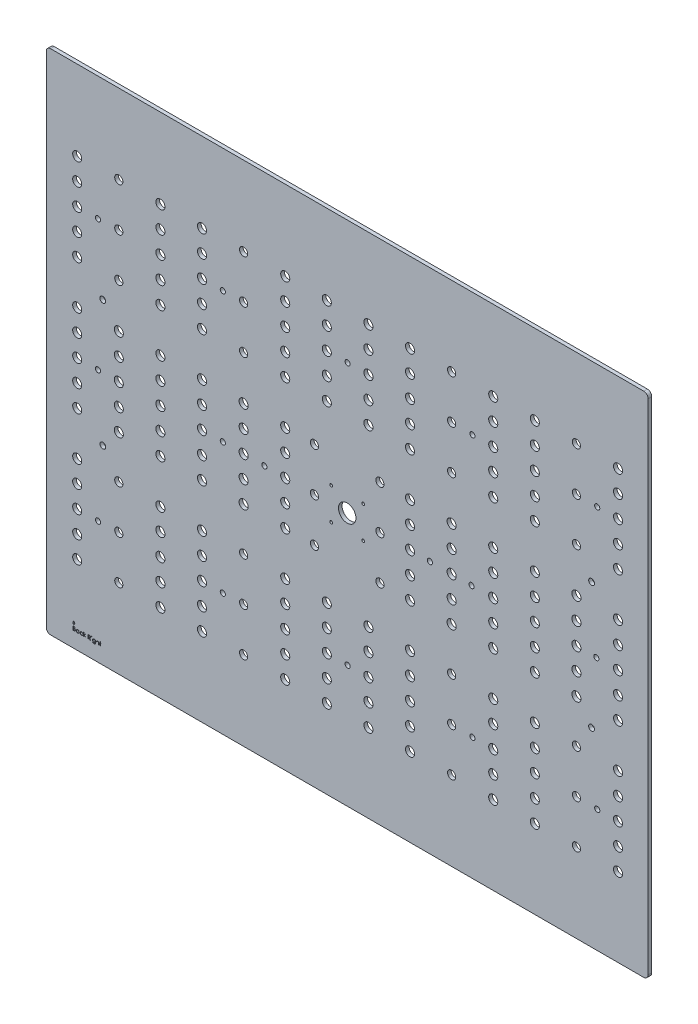
SolidWorks part; units mm, degrees
material "Acrylic (Medium-high impact)"
ref_plane "Front Plane" through (0, 0, 0) normal (0, 0, 1) x (1, 0, 0)
ref_plane "Top Plane" through (0, 0, 0) normal (0, 1, 0) x (1, 0, 0)
ref_plane "Right Plane" through (0, 0, 0) normal (1, 0, 0) x (0, 0, -1)
sketch "Sketch1" plane through (0, 0, 0) normal (0, 0, 1) x (1, 0, 0)
  line L1 (-119.7736, 224.7428) -> (458.2796, 224.7428)
  line L2 (-119.7736, 224.7428) -> (-119.7736, -271.111)
  line L3 (-119.7736, -271.111) -> (458.2796, -271.111)
  line L4 (458.2796, 224.7428) -> (458.2796, -271.111)
  dimension "D1" = 495.8537
  dimension "D2" = 578.0532
extrude "Boss-Extrude1" add sketch "Sketch1" along normal blind 3.175
sketch "Sketch8" plane through (0, 0, 3.175) normal (0, 0, 1) x (1, 0, 0)
  line L1 (-119.7736, 224.7428) -> (-100.3426, 224.7428)
  line L2 (-119.7736, 224.7428) -> (-119.7736, 205.3118)
  line L3 (-119.7736, 205.3118) -> (-100.3426, 205.3118)
  line L4 (-100.3426, 224.7428) -> (-100.3426, 205.3118)
  line L5 (458.2796, 224.7428) -> (438.8486, 224.7428)
  line L6 (458.2796, 224.7428) -> (458.2796, 205.3118)
  line L7 (458.2796, 205.3118) -> (438.8486, 205.3118)
  line L8 (438.8486, 224.7428) -> (438.8486, 205.3118)
  line L9 (458.2796, -271.111) -> (438.8486, -271.111)
  line L10 (458.2796, -271.111) -> (458.2796, -251.68)
  line L11 (458.2796, -251.68) -> (438.8486, -251.68)
  line L12 (438.8486, -271.111) -> (438.8486, -251.68)
  line L13 (-119.7736, -271.111) -> (-100.3426, -271.111)
  line L14 (-119.7736, -271.111) -> (-119.7736, -251.68)
  line L15 (-119.7736, -251.68) -> (-100.3426, -251.68)
  line L16 (-100.3426, -271.111) -> (-100.3426, -251.68)
  dimension "D1" = 19.431
extrude "Corners" cut sketch "Sketch8" against normal through all
sketch "Sketch9" plane through (0, 0, 3.175) normal (0, 0, 1) x (1, 0, 0)
  line L0 (-84.747, 138.1059) -> (423.253, 138.1059) construction
  line L1 (169.253, 224.7428) -> (169.253, -271.111) construction
  line L2 (438.8486, 224.7428) -> (-100.3426, 224.7428) construction
  line L3 (-100.3426, -271.111) -> (438.8486, -271.111) construction
  line L4 (140.678, 23.8059) -> (197.828, 23.8059) construction
  line L6 (-84.747, -213.6841) -> (423.253, -213.6841) construction
  line L7 (-84.747, -213.6841) -> (-84.747, 167.3159) construction
  line L8 (-84.747, 167.3159) -> (423.253, 167.3159) construction
  line L9 (423.253, -213.6841) -> (423.253, 167.3159) construction
  point P99 (169.253, 23.8059)
  dimension "D1" = 381
  dimension "D2" = 508
  dimension "D3" = 29.21
  dimension "D8" = 57.15
sketch "Sketch13" plane through (0, 0, 3.175) normal (0, 0, 1) x (1, 0, 0)
  line L0 (169.253, 224.7428) -> (169.253, -271.111) construction
  line L1 (438.8486, 224.7428) -> (-100.3426, 224.7428) construction
  line L2 (-100.3426, -271.111) -> (438.8486, -271.111) construction
  line L4 (155.283, -37.1541) -> (183.223, -37.1541) construction
  line L5 (155.283, -37.1541) -> (155.283, -9.2141) construction
  line L6 (155.283, -9.2141) -> (183.223, -9.2141) construction
  line L7 (183.223, -37.1541) -> (183.223, -9.2141) construction
  line L8 (155.283, -37.1541) -> (183.223, -9.2141) construction
  line L9 (155.283, -9.2141) -> (183.223, -37.1541) construction
  circle A0 centre (169.253, -23.1841) radius 7.62
  dimension "D1" = 15.24
  dimension "D2" = 27.94
extrude "camera hole" cut sketch "Sketch13" against normal through all
sketch "Sketch12" plane through (0, 0, 0) normal (0, 0, -1) x (-1, 0, 0)
  line L0 (-360.3499, 21.7739) -> (-360.3499, -68.1421) construction
  line L1 (-414.7821, 136.0739) -> (-396.6719, 136.0739) construction
  line L2 (-414.7821, 136.0739) -> (-414.7821, 46.1579) construction
  line L3 (-414.7821, 46.1579) -> (-396.6719, 46.1579) construction
  line L4 (-396.6719, 136.0739) -> (-396.6719, 46.1579) construction
  line L5 (-342.1381, 136.0739) -> (-324.0279, 136.0739) construction
  line L6 (-342.1381, 136.0739) -> (-342.1381, 46.1579) construction
  line L7 (-342.1381, 46.1579) -> (-324.0279, 46.1579) construction
  line L8 (-324.0279, 136.0739) -> (-324.0279, 46.1579) construction
  line L9 (-305.8161, 136.0739) -> (-287.7059, 136.0739) construction
  line L10 (-305.8161, 136.0739) -> (-305.8161, 46.1579) construction
  line L11 (-305.8161, 46.1579) -> (-287.7059, 46.1579) construction
  line L12 (-287.7059, 136.0739) -> (-287.7059, 46.1579) construction
  line L13 (-233.1721, 136.0739) -> (-215.0619, 136.0739) construction
  line L14 (-233.1721, 136.0739) -> (-233.1721, 46.1579) construction
  line L15 (-233.1721, 46.1579) -> (-215.0619, 46.1579) construction
  line L16 (-215.0619, 136.0739) -> (-215.0619, 46.1579) construction
  line L17 (-196.8501, 136.0739) -> (-178.7399, 136.0739) construction
  line L18 (-196.8501, 136.0739) -> (-196.8501, 46.1579) construction
  line L19 (-196.8501, 46.1579) -> (-178.7399, 46.1579) construction
  line L20 (-178.7399, 136.0739) -> (-178.7399, 46.1579) construction
  line L21 (-160.5281, 136.0739) -> (-142.4179, 136.0739) construction
  line L22 (-160.5281, 136.0739) -> (-160.5281, 46.1579) construction
  line L23 (-160.5281, 46.1579) -> (-142.4179, 46.1579) construction
  line L24 (-142.4179, 136.0739) -> (-142.4179, 46.1579) construction
  line L25 (-124.2061, 136.0739) -> (-106.0959, 136.0739) construction
  line L26 (-124.2061, 136.0739) -> (-124.2061, 46.1579) construction
  line L27 (-124.2061, 46.1579) -> (-106.0959, 46.1579) construction
  line L28 (-106.0959, 136.0739) -> (-106.0959, 46.1579) construction
  line L29 (-51.5621, 136.0739) -> (-33.4519, 136.0739) construction
  line L30 (-51.5621, 136.0739) -> (-51.5621, 46.1579) construction
  line L31 (-51.5621, 46.1579) -> (-33.4519, 46.1579) construction
  line L32 (-33.4519, 136.0739) -> (-33.4519, 46.1579) construction
  line L33 (-15.2401, 136.0739) -> (2.8701, 136.0739) construction
  line L34 (-15.2401, 136.0739) -> (-15.2401, 46.1579) construction
  line L35 (-15.2401, 46.1579) -> (2.8701, 46.1579) construction
  line L36 (2.8701, 136.0739) -> (2.8701, 46.1579) construction
  line L37 (57.4039, 136.0739) -> (75.5141, 136.0739) construction
  line L38 (57.4039, 136.0739) -> (57.4039, 46.1579) construction
  line L39 (57.4039, 46.1579) -> (75.5141, 46.1579) construction
  line L40 (75.5141, 136.0739) -> (75.5141, 46.1579) construction
  line L41 (-414.7821, -92.5261) -> (-396.6719, -92.5261) construction
  line L42 (-414.7821, -92.5261) -> (-414.7821, -182.4421) construction
  line L43 (-414.7821, -182.4421) -> (-396.6719, -182.4421) construction
  line L44 (-396.6719, -92.5261) -> (-396.6719, -182.4421) construction
  line L45 (-342.1381, -92.5261) -> (-324.0279, -92.5261) construction
  line L46 (-342.1381, -92.5261) -> (-342.1381, -182.4421) construction
  line L47 (-342.1381, -182.4421) -> (-324.0279, -182.4421) construction
  line L48 (-324.0279, -92.5261) -> (-324.0279, -182.4421) construction
  line L49 (-305.8161, -92.5261) -> (-287.7059, -92.5261) construction
  line L50 (-305.8161, -92.5261) -> (-305.8161, -182.4421) construction
  line L51 (-305.8161, -182.4421) -> (-287.7059, -182.4421) construction
  line L52 (-287.7059, -92.5261) -> (-287.7059, -182.4421) construction
  line L53 (-233.1721, -92.5261) -> (-215.0619, -92.5261) construction
  line L54 (-233.1721, -92.5261) -> (-233.1721, -182.4421) construction
  line L55 (-233.1721, -182.4421) -> (-215.0619, -182.4421) construction
  line L56 (-215.0619, -92.5261) -> (-215.0619, -182.4421) construction
  line L57 (-196.8501, -92.5261) -> (-178.7399, -92.5261) construction
  line L58 (-196.8501, -92.5261) -> (-196.8501, -182.4421) construction
  line L59 (-196.8501, -182.4421) -> (-178.7399, -182.4421) construction
  line L60 (-178.7399, -92.5261) -> (-178.7399, -182.4421) construction
  line L61 (-160.5281, -92.5261) -> (-142.4179, -92.5261) construction
  line L62 (-160.5281, -92.5261) -> (-160.5281, -182.4421) construction
  line L63 (-160.5281, -182.4421) -> (-142.4179, -182.4421) construction
  line L64 (-142.4179, -92.5261) -> (-142.4179, -182.4421) construction
  line L65 (-124.2061, -92.5261) -> (-106.0959, -92.5261) construction
  line L66 (-124.2061, -92.5261) -> (-124.2061, -182.4421) construction
  line L67 (-124.2061, -182.4421) -> (-106.0959, -182.4421) construction
  line L68 (-106.0959, -92.5261) -> (-106.0959, -182.4421) construction
  line L69 (-51.5621, -92.5261) -> (-33.4519, -92.5261) construction
  line L70 (-51.5621, -92.5261) -> (-51.5621, -182.4421) construction
  line L71 (-51.5621, -182.4421) -> (-33.4519, -182.4421) construction
  line L72 (-33.4519, -92.5261) -> (-33.4519, -182.4421) construction
  line L73 (-15.2401, -92.5261) -> (2.8701, -92.5261) construction
  line L74 (-15.2401, -92.5261) -> (-15.2401, -182.4421) construction
  line L75 (-15.2401, -182.4421) -> (2.8701, -182.4421) construction
  line L76 (2.8701, -92.5261) -> (2.8701, -182.4421) construction
  line L77 (57.4039, -92.5261) -> (75.5141, -92.5261) construction
  line L78 (57.4039, -92.5261) -> (57.4039, -182.4421) construction
  line L79 (57.4039, -182.4421) -> (75.5141, -182.4421) construction
  line L80 (75.5141, -92.5261) -> (75.5141, -182.4421) construction
  line L81 (-414.7821, 21.7739) -> (-396.6719, 21.7739) construction
  line L82 (-414.7821, 21.7739) -> (-414.7821, -68.1421) construction
  line L83 (-414.7821, -68.1421) -> (-396.6719, -68.1421) construction
  line L84 (-396.6719, 21.7739) -> (-396.6719, -68.1421) construction
  line L85 (-124.2061, 21.7739) -> (-106.0959, 21.7739) construction
  line L86 (-124.2061, 21.7739) -> (-124.2061, -68.1421) construction
  line L87 (-124.2061, -68.1421) -> (-106.0959, -68.1421) construction
  line L88 (-106.0959, 21.7739) -> (-106.0959, -68.1421) construction
  line L89 (-378.4601, 21.7739) -> (-360.3499, 21.7739) construction
  line L90 (-378.4601, 21.7739) -> (-378.4601, -68.1421) construction
  line L91 (-378.4601, -68.1421) -> (-360.3499, -68.1421) construction
  line L92 (-87.8841, 21.7739) -> (-69.7739, 21.7739) construction
  line L93 (-87.8841, 21.7739) -> (-87.8841, -68.1421) construction
  line L94 (-69.7739, 21.7739) -> (-69.7739, -68.1421) construction
  line L95 (-87.8841, -68.1421) -> (-69.7739, -68.1421) construction
  line L96 (-324.0279, 21.7739) -> (-324.0279, -68.1421) construction
  line L97 (-342.1381, 21.7739) -> (-324.0279, 21.7739) construction
  line L98 (-342.1381, 21.7739) -> (-342.1381, -68.1421) construction
  line L99 (-342.1381, -68.1421) -> (-324.0279, -68.1421) construction
  line L100 (-51.5621, 21.7739) -> (-33.4519, 21.7739) construction
  line L101 (-51.5621, 21.7739) -> (-51.5621, -68.1421) construction
  line L102 (-33.4519, 21.7739) -> (-33.4519, -68.1421) construction
  line L103 (-51.5621, -68.1421) -> (-33.4519, -68.1421) construction
  line L104 (-287.7059, 21.7739) -> (-287.7059, -68.1421) construction
  line L105 (-305.8161, 21.7739) -> (-287.7059, 21.7739) construction
  line L106 (-305.8161, 21.7739) -> (-305.8161, -68.1421) construction
  line L107 (-305.8161, -68.1421) -> (-287.7059, -68.1421) construction
  line L108 (-15.2401, 21.7739) -> (2.8701, 21.7739) construction
  line L109 (-15.2401, 21.7739) -> (-15.2401, -68.1421) construction
  line L110 (2.8701, 21.7739) -> (2.8701, -68.1421) construction
  line L111 (-15.2401, -68.1421) -> (2.8701, -68.1421) construction
  line L112 (-251.3839, 21.7739) -> (-251.3839, -68.1421) construction
  line L113 (-269.4941, 21.7739) -> (-251.3839, 21.7739) construction
  line L114 (-269.4941, 21.7739) -> (-269.4941, -68.1421) construction
  line L115 (-269.4941, -68.1421) -> (-251.3839, -68.1421) construction
  line L116 (21.0819, 21.7739) -> (39.1921, 21.7739) construction
  line L117 (21.0819, 21.7739) -> (21.0819, -68.1421) construction
  line L118 (39.1921, 21.7739) -> (39.1921, -68.1421) construction
  line L119 (21.0819, -68.1421) -> (39.1921, -68.1421) construction
  line L120 (-215.0619, 21.7739) -> (-215.0619, -68.1421) construction
  line L121 (-233.1721, 21.7739) -> (-215.0619, 21.7739) construction
  line L122 (-233.1721, 21.7739) -> (-233.1721, -68.1421) construction
  line L123 (-233.1721, -68.1421) -> (-215.0619, -68.1421) construction
  line L124 (57.4039, 21.7739) -> (75.5141, 21.7739) construction
  line L125 (57.4039, 21.7739) -> (57.4039, -68.1421) construction
  line L126 (75.5141, 21.7739) -> (75.5141, -68.1421) construction
  line L127 (57.4039, -68.1421) -> (75.5141, -68.1421) construction
  line L128 (-376.009, 137.4709) -> (-362.801, 137.4709) construction
  line L129 (-376.009, 44.7609) -> (-362.801, 44.7609) construction
  line L130 (-85.433, 137.4709) -> (-72.225, 137.4709) construction
  line L131 (-85.433, 44.7609) -> (-72.225, 44.7609) construction
  line L132 (23.533, 137.4709) -> (36.741, 137.4709) construction
  line L133 (23.533, 44.7609) -> (36.741, 44.7609) construction
  line L134 (-267.043, 137.4709) -> (-253.835, 137.4709) construction
  line L135 (-267.043, 44.7609) -> (-253.835, 44.7609) construction
  line L136 (23.533, -91.1291) -> (36.741, -91.1291) construction
  line L137 (23.533, -183.8391) -> (36.741, -183.8391) construction
  line L138 (-267.043, -91.1291) -> (-253.835, -91.1291) construction
  line L139 (-267.043, -183.8391) -> (-253.835, -183.8391) construction
  line L140 (-85.433, -91.1291) -> (-72.225, -91.1291) construction
  line L141 (-85.433, -183.8391) -> (-72.225, -183.8391) construction
  line L142 (-376.009, -91.1291) -> (-362.801, -91.1291) construction
  line L143 (-376.009, -183.8391) -> (-362.801, -183.8391) construction
  line L144 (-204.432, 18.4719) -> (-191.224, 18.4719) construction
  line L145 (-204.432, -74.2381) -> (-191.224, -74.2381) construction
  line L146 (-147.282, 18.4719) -> (-134.074, 18.4719) construction
  line L147 (-147.282, -74.2381) -> (-134.074, -74.2381) construction
  line L148 (66.459, -68.1421) -> (66.459, 21.7739) construction
  line L149 (66.459, 46.1579) -> (66.459, 136.0739) construction
  line L150 (30.137, 44.7609) -> (30.137, 137.4709) construction
  line L151 (75.5141, -137.4841) -> (-414.7821, -137.4841) construction
  line L152 (-458.2796, -251.68) -> (-458.2796, 205.3118) construction
  line L153 (75.5141, 91.1159) -> (-414.7821, 91.1159) construction
  line L154 (75.5141, -23.1841) -> (-414.7821, -23.1841) construction
  line L155 (-414.7821, -137.4841) -> (-414.7821, 136.0739) construction
  line L156 (75.5141, -182.4421) -> (75.5141, 136.0739) construction
  line L157 (42.837, -137.4841) -> (-382.105, -137.4841) construction
  line L158 (-414.7821, 136.0739) -> (75.5141, 136.0739) construction
  line L159 (100.3426, -271.111) -> (-438.8486, -271.111) construction
  line L160 (30.137, -183.8391) -> (30.137, -91.1291) construction
  line L161 (-382.105, 91.1159) -> (42.837, 91.1159) construction
  line L162 (-127.978, -23.1841) -> (-210.528, -23.1841) construction
  line L163 (-140.678, -74.2381) -> (-140.678, 18.4719) construction
  line L164 (-197.828, -74.2381) -> (-197.828, 18.4719) construction
  line L165 (84.747, -23.1841) -> (-423.253, -23.1841) construction
  line L166 (84.747, -213.6841) -> (84.747, 167.3159) construction
  line L167 (-423.253, -213.6841) -> (-423.253, 167.3159) construction
  circle A0 centre (30.137, 138.1059) radius 1.905 construction
  circle A1 centre (66.459, 52.5079) radius 3.9687
  circle A2 centre (66.459, 71.5579) radius 3.9688
  circle A3 centre (66.459, 90.6079) radius 3.9687
  circle A4 centre (66.459, 109.6579) radius 3.9687
  circle A5 centre (66.459, 128.7079) radius 3.9688
  spline S0 degree 2 poles (-362.801, 137.4709) (-350.609, 91.1159) (-362.801, 44.7609) knots 0 0 0 1 1 1 construction
  spline S1 degree 2 poles (-376.009, 137.4709) (-388.201, 91.1159) (-376.009, 44.7609) knots 0 0 0 1 1 1 construction
  spline S2 degree 2 poles (-72.225, 137.4709) (-60.033, 91.1159) (-72.225, 44.7609) knots 0 0 0 1 1 1 construction
  spline S3 degree 2 poles (-85.433, 137.4709) (-97.625, 91.1159) (-85.433, 44.7609) knots 0 0 0 1 1 1 construction
  spline S4 degree 2 poles (36.741, 137.4709) (48.933, 91.1159) (36.741, 44.7609) knots 0 0 0 1 1 1 construction
  spline S5 degree 2 poles (23.533, 137.4709) (11.341, 91.1159) (23.533, 44.7609) knots 0 0 0 1 1 1 construction
  spline S6 degree 2 poles (-253.835, 137.4709) (-241.643, 91.1159) (-253.835, 44.7609) knots 0 0 0 1 1 1 construction
  spline S7 degree 2 poles (-267.043, 137.4709) (-279.235, 91.1159) (-267.043, 44.7609) knots 0 0 0 1 1 1 construction
  spline S8 degree 2 poles (36.741, -91.1291) (48.933, -137.4841) (36.741, -183.8391) knots 0 0 0 1 1 1 construction
  spline S9 degree 2 poles (23.533, -91.1291) (11.341, -137.4841) (23.533, -183.8391) knots 0 0 0 1 1 1 construction
  spline S10 degree 2 poles (-253.835, -91.1291) (-241.643, -137.4841) (-253.835, -183.8391) knots 0 0 0 1 1 1 construction
  spline S11 degree 2 poles (-267.043, -91.1291) (-279.235, -137.4841) (-267.043, -183.8391) knots 0 0 0 1 1 1 construction
  spline S12 degree 2 poles (-72.225, -91.1291) (-60.033, -137.4841) (-72.225, -183.8391) knots 0 0 0 1 1 1 construction
  spline S13 degree 2 poles (-85.433, -91.1291) (-97.625, -137.4841) (-85.433, -183.8391) knots 0 0 0 1 1 1 construction
  spline S14 degree 2 poles (-362.801, -91.1291) (-350.609, -137.4841) (-362.801, -183.8391) knots 0 0 0 1 1 1 construction
  spline S15 degree 2 poles (-376.009, -91.1291) (-388.201, -137.4841) (-376.009, -183.8391) knots 0 0 0 1 1 1 construction
  spline S16 degree 2 poles (-204.432, 18.4719) (-216.7462, -27.7201) (-204.432, -74.2381) knots 0 0 0 1 1 1 construction
  spline S17 degree 2 poles (-191.224, 18.4719) (-178.9098, -27.7201) (-191.224, -74.2381) knots 0 0 0 1 1 1 construction
  spline S18 degree 2 poles (-147.282, 18.4719) (-159.5962, -27.7201) (-147.282, -74.2381) knots 0 0 0 1 1 1 construction
  spline S19 degree 2 poles (-134.074, 18.4719) (-121.7598, -27.7201) (-134.074, -74.2381) knots 0 0 0 1 1 1 construction
  dimension "D6" = 7.9375
  dimension "D7" = 6.35
  dimension "D10" = 89.916
  dimension "D9" = 490.2962
  dimension "D11" = 18.1102
  dimension "D12" = 89.916
  dimension "D13" = 89.916
  dimension "D14" = 18.1102
  dimension "D15" = 92.71
  dimension "D16" = 46.355
  dimension "D17" = 18.1102
  dimension "D18" = 92.71
  dimension "D19" = 114.3
  dimension "D1" = 6
  dimension "D2" = 2
  dimension "D3" = 2
  dimension "D4" = 2
  dimension "D5" = 2
  dimension "D8" = 5
extrude "LED holes" cut sketch "Sketch12" against normal through all
sketch "Sketch15" plane through (0, 0, 3.175) normal (0, 0, 1) x (1, 0, 0)
  line L0 (-100.3426, 224.7428) -> (438.8486, 224.7428)
  line L1 (438.8486, 224.7428) -> (438.8486, 205.3118)
  line L2 (438.8486, 205.3118) -> (458.2796, 205.3118)
  line L3 (458.2796, 205.3118) -> (458.2796, -251.68)
  line L4 (458.2796, -251.68) -> (438.8486, -251.68)
  line L5 (438.8486, -251.68) -> (438.8486, -271.111)
  line L6 (438.8486, -271.111) -> (-100.3426, -271.111)
  line L7 (-100.3426, -271.111) -> (-100.3426, -251.68)
  line L8 (-100.3426, -251.68) -> (-119.7736, -251.68)
  line L9 (-119.7736, -251.68) -> (-119.7736, 205.3118)
  line L10 (-119.7736, 205.3118) -> (-100.3426, 205.3118)
  line L11 (-100.3426, 205.3118) -> (-100.3426, 224.7428)
  line L12 (-99.8346, 224.2348) -> (438.3406, 224.2348)
  line L13 (438.3406, 224.2348) -> (438.3406, 204.8038)
  line L14 (438.3406, 204.8038) -> (457.7716, 204.8038)
  line L15 (457.7716, 204.8038) -> (457.7716, -251.172)
  line L16 (457.7716, -251.172) -> (438.3406, -251.172)
  line L17 (438.3406, -251.172) -> (438.3406, -270.603)
  line L18 (438.3406, -270.603) -> (-99.8346, -270.603)
  line L19 (-99.8346, -270.603) -> (-99.8346, -251.172)
  line L20 (-99.8346, -251.172) -> (-119.2656, -251.172)
  line L21 (-119.2656, -251.172) -> (-119.2656, 204.8038)
  line L22 (-119.2656, 204.8038) -> (-99.8346, 204.8038)
  line L23 (-99.8346, 204.8038) -> (-99.8346, 224.2348)
  dimension "D1" = 0.508
extrude "Cut-Extrude7" cut sketch "Sketch15" against normal through all
fillet "Fillet1" radius 2.54 8 edges at (-119.2656, 204.8038, 1.5875) (-99.8346, 224.2348, 1.5875) (438.3406, 224.2348, 1.5875) (457.7716, 204.8038, 1.5875) (457.7716, -251.172, 1.5875) (438.3406, -270.603, 1.5875) (-119.2656, -251.172, 1.5875) (-99.8346, -270.603, 1.5875)
sketch "Sketch17" plane through (0, 0, 0) normal (0, 0, -1) x (-1, 0, 0)
  line L0 (30.137, 44.7609) -> (30.137, 137.4709) construction
  line L1 (42.837, 91.1159) -> (17.437, 91.1159) construction
  circle A0 centre (30.137, 53.0159) radius 3.5719
  circle A1 centre (30.137, 91.1159) radius 3.5719
  circle A2 centre (30.137, 129.2159) radius 3.5719
  dimension "D2" = 7.1437
  dimension "D1" = 3
pattern_linear "LPattern1" count 14 spacing 36.322 along (1, 0, 0) count 3 spacing 114.3 along (0, -1, 0) skipping (1, 0), (1, 2), (4, 0), (4, 2), (6, 1), (7, 1), (9, 0), (9, 2), (12, 0), (12, 2) of "LED holes"
extrude "White LED" cut sketch "Sketch17" against normal through all
pattern_linear "LPattern3" count 3 spacing 228.6 along (0, -1, 0) count 12 spacing 36.322 along (1, 0, 0) skipping (0, 1), (0, 2), (0, 4), (0, 5), (0, 6), (0, 7), (0, 9), (0, 10), (1, 1), (1, 2), (1, 4), (1, 5), (1, 6), (1, 7), (1, 9), (1, 10) of "White LED"
sketch "Sketch18" plane through (0, 0, 0) normal (0, 0, -1) x (-1, 0, 0)
  line L0 (-140.678, -74.2381) -> (-140.678, 18.4719) construction
  line L1 (-147.282, -74.2381) -> (-134.074, -74.2381) construction
  line L2 (-147.282, 18.4719) -> (-134.074, 18.4719) construction
  line L3 (-197.828, -74.2381) -> (-197.828, 18.4719) construction
  line L4 (-204.432, -74.2381) -> (-191.224, -74.2381) construction
  line L5 (-204.432, 18.4719) -> (-191.224, 18.4719) construction
  line L6 (-115.151, -61.7921) -> (-140.678, -61.7921) construction
  circle A0 centre (-140.678, -61.7921) radius 3.5719
  circle A1 centre (-197.828, -61.7921) radius 3.5719
  circle A2 centre (-197.828, -23.6921) radius 3.5719
  circle A3 centre (-197.828, 14.4079) radius 3.5719
  circle A4 centre (-140.678, -23.6921) radius 3.5719
  circle A5 centre (-140.678, 14.4079) radius 3.5719
  dimension "D1" = 7.1437
  dimension "D2" = 2
  dimension "D3" = 3
extrude "White LED2" cut sketch "Sketch18" against normal through all
hole_wizard "#8 Clearance Hole light strap" positions "Sketch20" profile "Sketch21" hole size "#8" standard "ANSI Inch" end condition through all
sketch "Sketch20" plane through (0, 0, 0) normal (0, 0, -1) x (-1, 0, 0)
  line L7 (66.459, 128.7079) -> (66.459, 52.5079) construction
  line L17 (-438.3406, 204.8038) -> (-438.3406, -251.172) construction
  line L26 (-169.253, 224.2348) -> (-169.253, -270.603) construction
  line L27 (-435.8006, 224.2348) -> (97.2946, 224.2348) construction
  line L28 (97.2946, -270.603) -> (-435.8006, -270.603) construction
  point P32 (48.298, 90.6079)
  point P87 (48.298, -137.9921)
  dimension "D1" = 228.6
  dimension "D2" = 217.551
  dimension "D3" = 38.1
sketch "Sketch21" plane through (-48.298, 90.6079, 0) normal (1, 0, 0) x (0, 1, 0)
  line L0 (0, 0) -> (0, 3.175)
  line L1 (0, 3.175) -> (2.2479, 3.175)
  line L2 (2.2479, 3.175) -> (2.2479, 0)
  line L5 (2.2479, 0) -> (0, 0)
  line L11 (0, -6.35) -> (0, 107.95) construction
  dimension "Thru Hole Dia." = 4.4958
  dimension "Thru Hole Depth" = 3.175
hole_wizard "#2 Clearance Hole Camera Mount" positions "Sketch22" profile "Sketch23" hole size "#2" standard "ANSI Inch" end condition through all
sketch "Sketch22" plane through (0, 0, 3.175) normal (0, 0, 1) x (1, 0, 0)
  point P0 (155.283, -9.2141)
  point P3 (183.223, -9.2141)
  point P6 (183.223, -37.1541)
  point P9 (155.283, -37.1541)
sketch "Sketch23" plane through (155.283, -9.2141, 3.175) normal (1, 0, 0) x (0, -1, 0)
  line L0 (0, 0) -> (0, 3.175)
  line L1 (0, 3.175) -> (1.2192, 3.175)
  line L2 (1.2192, 3.175) -> (1.2192, 0)
  line L5 (1.2192, 0) -> (0, 0)
  line L11 (0, -6.35) -> (0, 107.95) construction
  dimension "Thru Hole Dia." = 2.4384
  dimension "Thru Hole Depth" = 3.175
pattern_linear "LPattern7" count 5 spacing 108.966 along (1, 0, 0) of "#8 Clearance Hole light strap"
hole_wizard "#8 Clearance Hole Strap holes" positions "Sketch24" profile "Sketch25" hole size "#8" standard "ANSI Inch" end condition through all
sketch "Sketch24" plane through (0, 0, 3.175) normal (0, 0, 1) x (1, 0, 0)
  line L0 (-48.298, 90.6079) -> (-48.298, -137.9921) construction
  line L3 (169.253, 224.7428) -> (169.253, -271.111) construction
  point P0 (-48.298, -23.6921)
  point P14 (60.668, -23.6921)
  point P16 (96.99, -23.6921)
  point P27 (241.516, -23.6921)
  point P28 (277.838, -23.6921)
  point P29 (386.804, -23.6921)
  dimension "D1" = 108.966
  dimension "D2" = 36.322
sketch "Sketch25" plane through (-48.298, -23.6921, 3.175) normal (1, 0, 0) x (0, -1, 0)
  line L0 (0, 0) -> (0, 3.175)
  line L1 (0, 3.175) -> (2.2479, 3.175)
  line L2 (2.2479, 3.175) -> (2.2479, 0)
  line L5 (2.2479, 0) -> (0, 0)
  line L11 (0, -6.35) -> (0, 107.95) construction
  dimension "Thru Hole Dia." = 4.4958
  dimension "Thru Hole Depth" = 3.175
sketch "Sketch26" plane through (0, 0, 3.175) normal (0, 0, 1) x (1, 0, 0)
  line L0 (169.253, 198.4538) -> (169.253, -244.822) construction
  line L1 (-93.4782, 198.4538) -> (431.9843, 198.4538)
  line L2 (-93.4782, 198.4538) -> (-93.4782, -244.822)
  line L3 (-93.4782, -244.822) -> (431.9843, -244.822)
  line L4 (431.9843, 198.4538) -> (431.9843, -244.822)
  line L5 (-149.9031, 273.5856) -> (501.3688, 273.5856)
  line L6 (-149.9031, 273.5856) -> (-149.9031, -302.1056)
  line L7 (-149.9031, -302.1056) -> (501.3688, -302.1056)
  line L8 (501.3688, 273.5856) -> (501.3688, -302.1056)
  line L9 (169.253, 224.7428) -> (169.253, -271.111) construction
  line L10 (-93.4782, -23.1841) -> (431.9843, -23.1841) construction
  circle A1 centre (169.253, -23.1841) radius 7.62 construction
  point P14 (169.253, -23.1841)
  dimension "D1" = 525.4625
  dimension "D2" = 443.2757
extrude "Outer Cimensions (temp)" cut sketch "Sketch26" against normal through all
fillet "Fillet2" radius 3.81 4 edges at (-93.4782, -244.822, 1.5875) (431.9843, -244.822, 1.5875) (431.9843, 198.4538, 1.5875) (-93.4782, 198.4538, 1.5875)
hole_wizard "#10 Clearance Hole1" positions "Sketch27" profile "Sketch28" hole size "#10" standard "ANSI Inch" end condition through all
sketch "Sketch27" plane through (0, 0, 3.175) normal (0, 0, 1) x (1, 0, 0)
  line L1 (-99.8282, -23.6921) -> (438.3343, -23.6921) construction
  line L4 (169.253, -244.822) -> (169.253, 198.4538) construction
  line L5 (-89.6682, -244.822) -> (428.1743, -244.822) construction
  line L6 (428.1743, 198.4538) -> (-89.6682, 198.4538) construction
  line L17 (-66.459, -61.7921) -> (-66.459, -99.8921) construction
  line L20 (6.185, -176.0921) -> (42.507, -176.0921) construction
  line L29 (-66.459, -23.6921) -> (42.507, -23.6921) construction
  point P70 (-44.107, -78.7932)
  point P152 (382.613, -78.7932)
  point P166 (382.613, 31.409)
  point P168 (-44.107, 31.409)
  dimension "D1" = 97.2989
  dimension "D2" = 213.36
sketch "Sketch28" plane through (-44.107, -78.7932, 3.175) normal (1, 0, 0) x (0, -1, 0)
  line L0 (0, 0) -> (0, 3.175)
  line L1 (0, 3.175) -> (2.5527, 3.175)
  line L2 (2.5527, 3.175) -> (2.5527, 0)
  line L5 (2.5527, 0) -> (0, 0)
  line L11 (0, -6.35) -> (0, 107.95) construction
  dimension "Thru Hole Dia." = 5.1054
  dimension "Thru Hole Depth" = 3.175
sketch "Sketch29" plane through (0, 0, 3.175) normal (0, 0, 1) x (1, 0, 0)
  line L0 (-70.4277, -176.0921) -> (-70.4277, -244.822) construction
  line L1 (-89.6682, -244.822) -> (428.1743, -244.822) construction
  line L2 (-70.4277, -231.5337) -> (7.8437, -231.5337) construction
  line L3 (-69.4117, -212.0184) -> (-69.4117, -220.8759) construction
  line L4 (-69.4117, -224.2083) -> (-70.4277, -225.4783)
  line L5 (-70.4277, -225.4783) -> (-69.9197, -225.4783)
  line L6 (-69.9197, -225.4783) -> (-69.9197, -226.7483)
  line L7 (-69.9197, -226.7483) -> (-68.9037, -226.7483)
  line L8 (-68.9037, -225.4783) -> (-68.9037, -226.7483)
  line L9 (-68.3957, -225.4783) -> (-68.9037, -225.4783)
  line L10 (-69.4117, -224.2083) -> (-68.3957, -225.4783)
  line L11 (-70.4277, -228.0183) -> (-51.1852, -228.0183) construction
  circle A0 centre (-66.459, -176.0921) radius 3.9687 construction
  text T0 "Back Right"
  point P13 (-69.4117, -226.7483)
  point P18 (-69.4117, -226.7483)
  dimension "D1" = 1.016
  dimension "D2" = 2.032
  dimension "D3" = 1.27
  dimension "D4" = 1.27
  dimension "D5" = 1.27
extrude "Cut-Extrude8" cut sketch "Sketch29" against normal blind 1.27
equation "\"Height\"= 32in"
equation "\"Width\"= 23in"
equation "\"Depth\"= 20in"
equation "\"Plexi\"= .121in"
equation "\"EBWidth\" = 9in"
equation "\"ComponentMountDia\"=0.1770"
equation "\"MagnetThickness\"= 0.125in"
equation "\"MagnetDiameter\"= 12mm"
equation "\"DoorPlexi\" = \"Plexi\""
equation "\"ShelfThickness\" = .1250in"
equation "\"BasePlateThickness\" = 0.5in"
equation "\"BasePlateWidth\" = \"Width\"+\"EBWidth\"-2*\"Plexi\""
equation "\"BasePlateDepth\" = \"TopBarDepth\"+2*\"CornerCube\""
equation "\"Boxsize\" = .75in"
equation "\"BoxsizeHalf\" = \"Boxsize\"/2"
equation "\"Boxinner\" = .625in"
equation "\"CornerCube\" = 0.75in"
equation "\"FingerLength\" = 1.125in"
equation "\"FingerWidth\" = .625in"
equation "\"Cutwidth\"= .016in"
equation "\"Earsize\"= 1in + \"Cutwidth\" /2"
equation "\"Slotsize\" = 1in - \"CutWidth\" / 2"
equation "\"InnerWidth\" = \"Width\" - 2* \"Plexi\""
equation "\"InnerHeight\" = \"Height\" -2 * \"Plexi\""
equation "\"InnerDepth\" = \"Depth\" - 2*\"Plexi\""
equation "\"FrontDoorGap\" = .1in"
equation "\"TopDepth\" = \"Depth\"-\"DoorPlexi\"-\"FrontDoorGap\""
equation "\"TopBarDepth\" = \"Depth\"-\"DoorPlexi\"-\"Plexi\"-2*\"MagnetThickness\"-2*\"CornerCube\""
equation "\"RearNumHoles\" = 4"
equation "\"RearHolesBorder\" = 2.25"
equation "\"RearHoleSpacing\" = (\"Width\" - 2*\"RearHolesBorder\") / (\"RearNumHoles\"-1)"
equation "\"RearBarLength\" = (\"InnerWidth\"-2*\"CornerCube\")"
equation "\"RearTopNumHoles\" = 4"
equation "\"RearTopHolesBorder\" = 3.1"
equation "\"RearTopHolesSpacing\" = (\"Width\" - 2*\"RearTopHolesBorder\") / (\"RearTopNumHoles\"-1)"
equation "\"SideTopNumHoles\" = 4"
equation "\"SideTopHoleOffset\"=\"CornerCube\"+\"FingerLength\"+\"Plexi\"+.5"
equation "\"SideTopHoleSpacing\" = (\"TopBarDepth\"-2*\"SideTopHoleOffset\") / (\"SideTopNumHoles\"-1)"
equation "\"SideHorizNumHoles\" = 4"
equation "\"SideHorizHoleBorder\" = 1.50"
equation "\"SideHorizHoleSpacing\" = (\"TopBarDepth\"-2*\"SideHorizHoleBorder\") / (\"SideHorizNumHoles\"-1)"
equation "\"SideVertBarLength\"=\"Height\"-\"BasePlateThickness\"-2*\"CornerCube\"-\"Plexi\""
equation "\"SideVertNumHoles\" = 4"
equation "\"SideVertHolesBorder\" = \"CornerCube\"+\"FingerLength\"+1.50"
equation "\"SideVertHoleSpacing\" = (\"SideVertBarLength\" - 2*(\"SideVertHolesBorder\"-\"Plexi\"-\"CornerCube\")) / (\"SideVertNumHoles\"-1)"
equation "\"RearSideVertNumHoles\" = 4"
equation "\"RearSideVertHolesBorder\" = 2.4"
equation "\"RearSideVertHoleSpacing\" = (\"SideVertBarLength\" - 2*(\"RearSideVertHolesBorder\"-\"Plexi\"-\"CornerCube\")) / (\"RearSideVertNumHoles\"-1)"
equation "\"Rivet3_16Dia\" = .191in"
equation "\"RivetDia\" = .228in"
equation "\"BinderPostDia\" = .228in"
equation "\"SlotDepth\" = \"Plexi\" + 0.75in + .005in"
equation "\"SideSlotWidth\"   = \"Plexi\"+.005in"
equation "\"SidePanelVertSpacing\" = (\"Height\"-2*(1.75-\"Plexi\")) / 5"
equation "\"BottomPanelSideHoleSpacing\" = (\"InnerDepth\"-2*(1.75-\"Plexi\")) / 4"
equation "\"CoolerDepth\" = 12in"
equation "\"ShelfGap\" = 0.5in"
equation "\"ShelfDepth\" = \"TopBarDepth\"+\"CornerCube\"-\"CoolerDepth\""
equation "\"ShelfBarDepth\"=\"ShelfDepth\"-2*\"CornerCube\""
equation "\"ShelfWidth\" = \"EBWidth\"-\"ShelfGap\""
equation "\"ShelfBarWidth\" = \"EBWidth\"-\"Boxsize\""
equation "\"ShelfBarWidthShort\" = \"ShelfBarWidth\"-\"Boxsize\"-\"ShelfGap\""
equation "\"ShelfHeight1\" = 13in"
equation "\"ShelfHeight2\" = 24in"
equation "\"IntakeWidth\"=4in"
equation "\"IntakeHeight\"=2in"
equation "\"ExhaustWidth\"=4in"
equation "\"ExhaustHeight\"=2in"
equation "\"VentSpacing\"=7in"
equation "\"VentVertLocation\"=12.75in"
equation "\"AngleBracketLengthShort\"=.625in"
equation "\"AngleBracketLengthLong\"=1in"
equation "\"AngleBracketWidth\"=.5in"
equation "\"AngleBracketThickness\"=.125in"
equation "\"AngleBracketHolePosShort\"=.358in"
equation "\"AngleBracketHolePosLong\"=.7in"
equation "\"AngleBracketHoleDia\"=\"Rivet3_16Dia\""
equation "\"ShelfBarAngleHole\"=\"ShelfGap\"+\"Boxsize\"+\"AngleBracketHolePosShort\""
equation "\"PSBracketThickness\" = .0641in"
equation "\"EBForwardMountOffset\" = 4.0in"
equation "\"EBForwardMount\" = 2*\"Boxsize\"+\"CoolerDepth\"+\"EBForwardMountOffset\""
equation "\"EBRearwardMountOffset\" = 1.5in"
equation "\"EBRearwardMount\"= \"Boxsize\"+\"EBRearwardMountOffset\""
equation "\"MagSealWidth\" = \"InnerWidth\""
equation "\"MagSealHeight\" = \"Height\"-\"BasePlateThickness\"-\"Plexi\""
equation "\"MagWidth\" = .500in"
equation "\"SiliconeSealOD\" = .3125in"
equation "\"SiliconeSealID\" = .1875in"
equation "\"SiliconeSealWidth\" = \"MagSealWidth\" - 2*\"MagWidth\"-\"SiliconeSealOD\""
equation "\"SiliconeSealHeigth\" = \"MagSealHeight\" - 2*\"MagWidth\"-\"SiliconeSealOD\""
equation "\"HooknLoopThick\" = .085in"
equation "\"HooknLoopWidth\" = 0.75in"
equation "\"HooknLoopHeigth\" = 0.75in"
equation "\"D1@Sketch8\"=\"Boxsize\"+.015"
equation "\"LightStrapHolesNum\"=4"
equation "\"D1@LPattern5\"=5"
equation "\"LightstrapHolesSpacing\"=4.29"
equation "\"D3@LPattern5\"= \"LightstrapHolesSpacing\""
